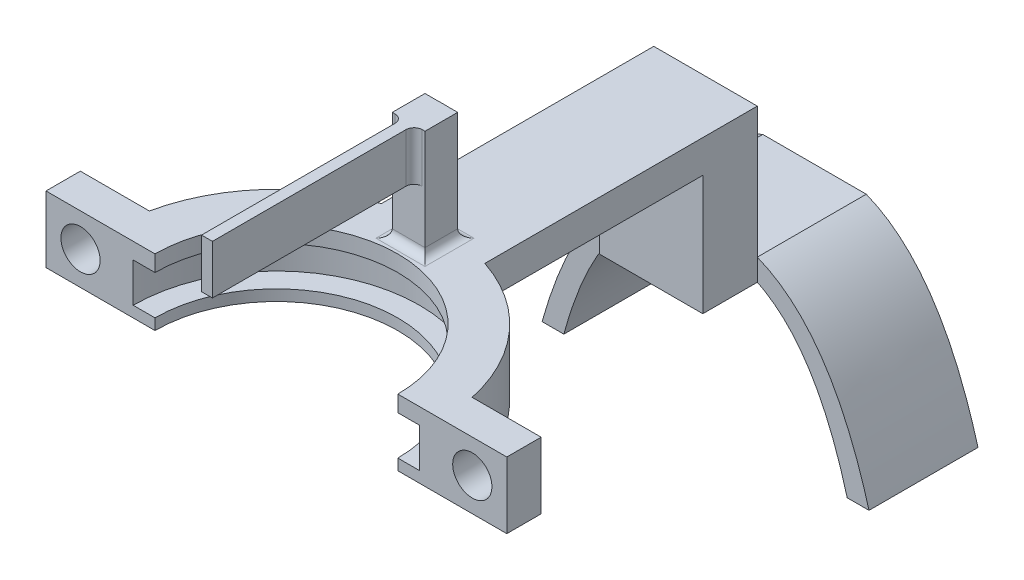
SolidWorks part; units mm, degrees
ref_plane "Front Plane" through (0, 0, 0) normal (0, 0, 1) x (1, 0, 0)
ref_plane "Top Plane" through (0, 0, 0) normal (0, 1, 0) x (1, 0, 0)
ref_plane "Right Plane" through (0, 0, 0) normal (1, 0, 0) x (0, 0, -1)
sketch "Sketch3" plane through (0, 0, 0) normal (0, 0, 1) x (1, 0, 0)
  line L2 (-62.6943, 11.7337) -> (-64.8845, 11.7337)
  line L3 (-62.8845, 10.2507) -> (-60.8845, 10.2507)
  line L5 (-60.8845, 6.6507) -> (-62.8845, 6.6507)
  line L6 (-62.8845, 6.6507) -> (-62.8845, 10.2507)
  line L10 (-64.8845, 11.7337) -> (-64.8845, 5.6398)
  line L11 (-64.8845, 5.6398) -> (-60.8845, 5.6398)
  line L12 (-60.8845, 5.6398) -> (-60.8845, 6.6507)
  line L13 (-60.8845, 10.2507) -> (-60.8845, 11.7337)
  line L14 (-60.8845, 11.7337) -> (-62.6943, 11.7337)
  dimension "D2" = 2
  dimension "D3" = 4
  dimension "D1" = 2
sketch "Sketch4" plane through (0, 0, 0) normal (0, 0, 1) x (1, 0, 0)
  line L0 (-49.7443, 0) -> (-49.7443, 12.8648) construction
  line L1 (27.6543, 0) -> (-27.6543, 0) construction
revolve "Revolve1" add sketch "Sketch3" angle 360 about L0
sketch "Sketch7" plane through (0, 11.7337, 0) normal (0, 1, 0) x (1, 0, 0)
  line L2 (-50.2443, 15.132) -> (-50.2443, 13.1308)
  line L3 (-49.2443, 15.132) -> (-49.2443, 13.1308)
  circle A0 centre (-49.7443, 0) radius 15.1403 construction
  arc A1 (-49.2443, 15.132) -> (-50.2443, 15.132) centre (-49.7443, 0) ccw
  circle A2 centre (-49.7443, 0) radius 13.1403 construction
  arc A3 (-49.2443, 13.1308) -> (-50.2443, 13.1308) centre (-49.7443, 0) ccw
  point P9 (-49.7443, 14.131)
  dimension "D1" = 1
extrude "Boss-Extrude1" add sketch "Sketch7" along normal blind 8.5
sketch "Sketch8" plane through (0, 20.2337, 0) normal (0, 1, 0) x (1, 0, 0)
  line L0 (-50.2443, 15.132) -> (-50.2443, 13.1308) construction
  line L3 (-50.2443, 15.132) -> (-50.2443, 13.1308)
  line L4 (-49.2443, 13.1308) -> (-49.2443, 15.132) construction
  line L5 (-49.2443, 13.1308) -> (-49.2443, 15.132)
  line L6 (-50.2443, 13.1308) -> (-50.2443, -6.3692)
  line L7 (-50.2443, -6.3692) -> (-49.2443, -6.3692)
  line L8 (-49.2443, -6.3692) -> (-49.2443, 13.1308)
  arc A0 (-49.2443, 15.132) -> (-50.2443, 15.132) centre (-49.7443, 0) ccw construction
  arc A1 (-49.2443, 15.132) -> (-50.2443, 15.132) centre (-49.7443, 0) ccw
  dimension "D1" = 19.5
extrude "Boss-Extrude2" add sketch "Sketch8" against normal blind 3
sketch "Sketch9" plane through (0, 11.7337, 0) normal (0, 1, 0) x (1, 0, 0)
  line L2 (-54.4943, 14.3759) -> (-54.4943, 39.3759)
  line L3 (-54.4943, 39.3759) -> (-44.9943, 39.3759)
  line L4 (-44.9943, 39.3759) -> (-44.9943, 14.3759)
  arc A0 (-50.2443, 15.132) -> (-49.2443, 15.132) centre (-49.7443, 0) ccw construction
  arc A1 (-50.2443, 15.132) -> (-54.4943, 14.3759) centre (-49.7443, 0) ccw
  arc A2 (-49.2443, 15.132) -> (-50.2443, 15.132) centre (-49.7443, 0) ccw construction
  arc A3 (-49.2443, 15.132) -> (-50.2443, 15.132) centre (-49.7443, 0) ccw
  arc A4 (-44.9943, 14.3759) -> (-49.2443, 15.132) centre (-49.7443, 0) ccw
  point P9 (-49.7443, 0)
  dimension "D1" = 25
extrude "Boss-Extrude3" add sketch "Sketch9" against normal blind 3
sketch "Sketch10" plane through (0, 8.7337, 0) normal (0, -1, 0) x (1, 0, 0)
  line L0 (-44.9943, -14.3759) -> (-44.9943, -39.3759) construction
  line L1 (-54.4943, -39.3759) -> (-44.9943, -39.3759)
  line L2 (-54.4943, -39.3759) -> (-54.4943, -34.3759)
  line L3 (-54.4943, -34.3759) -> (-44.9943, -34.3759)
  line L4 (-44.9943, -39.3759) -> (-44.9943, -34.3759)
  dimension "D1" = 5
extrude "Boss-Extrude4" add sketch "Sketch10" along normal blind 11
sketch "Sketch11" plane through (0, 0, -39.3759) normal (0, 0, -1) x (-1, 0, 0)
  line L0 (54.4943, -2.2663) -> (54.4943, 11.7337) construction
  line L1 (44.9943, -2.2663) -> (54.4943, -2.2663)
  line L2 (44.9943, -2.2663) -> (44.9943, -0.2663)
  line L3 (44.9943, -0.2663) -> (54.4943, -0.2663)
  line L4 (54.4943, -2.2663) -> (54.4943, -0.2663)
  dimension "D1" = 2
extrude "Boss-Extrude5" add sketch "Sketch11" along normal blind 10
sketch "Sketch13" plane through (0, 11.7337, 0) normal (0, 1, 0) x (1, 0, 0)
  line L2 (-49.7443, 3.15) -> (-49.7443, -3.15) construction
  line L3 (-28.604, 3.15) -> (-34.9353, 3.15)
  line L4 (-70.8845, 3.15) -> (-70.8845, -3.15)
  line L5 (-70.8845, -3.15) -> (-64.5532, -3.15)
  line L6 (-28.604, -3.15) -> (-28.604, 3.15)
  line L7 (-64.5532, 3.15) -> (-70.8845, 3.15)
  line L8 (-34.9353, -3.15) -> (-28.604, -3.15)
  arc A0 (-54.4943, 14.3759) -> (-44.9943, 14.3759) centre (-49.7443, 0) ccw construction
  arc A1 (-64.5532, 3.15) -> (-64.5532, -3.15) centre (-49.7443, 0) ccw
  arc A2 (-34.9353, -3.15) -> (-34.9353, 3.15) centre (-49.7443, 0) ccw
  point P10 (-49.7443, 0)
  point P13 (-49.7443, 3.15)
  dimension "D1" = 6.3
extrude "Boss-Extrude6" add sketch "Sketch13" against normal up to surface (6.0939 mm away) up to face at (-49.7443, 5.6398, -11.1403)
sketch "Sketch14" plane through (0, 0, 3.15) normal (0, 0, 1) x (1, 0, 0)
  line L0 (-70.8845, 11.7337) -> (-64.5532, 5.6398) construction
  line L1 (-28.604, 11.7337) -> (-34.9353, 5.6398) construction
  circle A0 centre (-31.7697, 8.6868) radius 1.8
  circle A1 centre (-67.7189, 8.6868) radius 1.8
  dimension "D1" = 3.6
  dimension "D2" = 3.6
extrude "Cut-Extrude1" cut sketch "Sketch14" against normal up to surface (6.3 mm away) contours A1 | A0 up to face at (-67.7189, 8.6868, -3.15)
sketch "Sketch15" plane through (0, 11.7337, 0) normal (0, 1, 0) x (1, 0, 0)
  line L0 (-70.8845, 0) -> (-23.4421, 0) construction
  line L1 (-70.8845, 3.15) -> (-70.8845, -3.15) construction
  line L2 (-7.0756, 0) -> (7.0756, 0) construction
  line L4 (-23.4421, 0) -> (-74.5953, 0)
  line L5 (-23.4421, 0) -> (-23.4421, -21.2106)
  line L6 (-23.4421, -21.2106) -> (-74.5953, -21.2106)
  line L7 (-74.5953, 0) -> (-74.5953, -21.2106)
extrude "Cut-Extrude3" cut sketch "Sketch15" against normal through all
sketch "Sketch16" plane through (0, 0, 0) normal (0, 1, 0) x (1, 0, 0)
  line L1 (-54.8883, 5.4174) -> (-45.2843, 5.4174)
  line L2 (-54.8883, 5.4174) -> (-54.8883, -6.4675)
  line L3 (-54.8883, -6.4675) -> (-45.2843, -6.4675)
  line L4 (-45.2843, 5.4174) -> (-45.2843, -6.4675)
sketch "Sketch18" plane through (0, 11.7337, 0) normal (0, 1, 0) x (1, 0, 0)
  line L0 (-50.2443, 15.132) -> (-49.2443, 15.132) construction
  line L1 (-48.2443, 15.132) -> (-51.2443, 15.132)
  line L2 (-51.2443, 15.132) -> (-51.2443, 12.132)
  line L3 (-51.2443, 12.132) -> (-48.2443, 12.132)
  line L4 (-48.2443, 12.132) -> (-48.2443, 15.132)
  point P7 (-49.7443, 15.132)
  dimension "D1" = 3
  dimension "D2" = 3
extrude "Boss-Extrude7" add sketch "Sketch18" along normal up to surface (8.5 mm away) up to face at (-49.7443, 20.2337, -4.3834)
fillet "Fillet1" radius 0.75 6 edges at (-49.7443, 11.7337, -12.132) (-48.7443, 11.7337, -15.132) (-49.7443, 11.7337, -15.1403) (-50.7443, 11.7337, -15.132) (-51.2443, 11.7337, -13.632) (-48.2443, 11.7337, -13.632)
sketch "Sketch19" plane through (0, 20.2337, 0) normal (0, 1, 0) x (1, 0, 0)
  line L18 (-50.2443, 15.132) -> (-51.2443, 15.132)
  line L19 (-51.2443, 15.132) -> (-51.2443, 12.132)
  line L20 (-51.2443, 12.132) -> (-50.2443, 12.132)
  line L21 (-50.2443, 12.132) -> (-50.2443, -6.3692)
  line L22 (-50.2443, -6.3692) -> (-49.2443, -6.3692)
  line L23 (-49.2443, -6.3692) -> (-49.2443, 12.132)
  line L24 (-49.2443, 12.132) -> (-48.2443, 12.132)
  line L25 (-48.2443, 12.132) -> (-48.2443, 15.132)
  line L26 (-48.2443, 15.132) -> (-49.2443, 15.132)
  line L27 (-50.2443, 15.132) -> (-51.2443, 15.132)
  line L28 (-51.2443, 15.132) -> (-51.2443, 12.132)
  line L29 (-51.2443, 12.132) -> (-50.2443, 12.132)
  line L30 (-50.2443, 12.132) -> (-50.2443, -6.3692)
  line L31 (-50.2443, -6.3692) -> (-49.2443, -6.3692)
  line L32 (-49.2443, -6.3692) -> (-49.2443, 12.132)
  line L33 (-49.2443, 12.132) -> (-48.2443, 12.132)
  line L34 (-48.2443, 12.132) -> (-48.2443, 15.132)
  line L35 (-48.2443, 15.132) -> (-49.2443, 15.132)
  arc A2 (-49.2443, 15.132) -> (-50.2443, 15.132) centre (-49.7443, 0) ccw
  arc A3 (-49.2443, 15.132) -> (-50.2443, 15.132) centre (-49.7443, 0) ccw
  dimension "D1" = 0
extrude "Boss-Extrude8" add sketch "Sketch19" along normal blind 1.5
fillet "Fillet2" radius 0.75 2 edges at (-49.2443, 19.4837, -12.132) (-50.2443, 19.4837, -12.132)
sketch "Sketch20" plane through (0, 0, -49.3759) normal (0, 0, -1) x (-1, 0, 0)
  line L0 (49.7443, -0.2663) -> (49.7443, -6.1882) construction
  line L1 (54.4943, -0.2663) -> (44.9943, -0.2663) construction
  line L2 (64.7443, -15.2663) -> (34.7443, -15.2663) construction
  line L4 (34.7443, -15.2663) -> (36.7443, -15.2663)
  line L5 (62.7443, -15.2663) -> (64.7443, -15.2663)
  line L8 (44.9943, -2.2663) -> (54.4943, -2.2663)
  line L9 (44.9943, -0.2663) -> (54.4943, -0.2663)
  line L11 (54.4943, -0.2663) -> (44.9943, -0.2663) construction
  line L12 (49.7443, -2.2663) -> (49.7443, -15.2663) construction
  spline S0 degree 2 poles (34.7443, -15.2663) (38.1968, -2.9668) (44.9943, -0.2663) knots 0 0 0 0.63993 0.63993 0.63993
  spline S1 degree 2 poles (36.7443, -15.2663) (39.5823, -4.8701) (44.9943, -2.2663) knots 0 0 0 0.599407 0.599407 0.599407
  spline S3 degree 2 poles (64.7443, -15.2663) (61.2918, -2.9668) (54.4943, -0.2663) knots 0 0 0 0.63993 0.63993 0.63993
  spline S4 degree 2 poles (54.4943, -2.2663) (59.9062, -4.8701) (62.7443, -15.2663) knots 0.400593 0.400593 0.400593 1 1 1
  point P7 (49.7443, -15.2663)
  dimension "D3" = 2
  dimension "D1" = 15
  dimension "D2" = 30
  dimension "D4" = 2
extrude "Boss-Extrude9" add sketch "Sketch20" against normal blind 10
